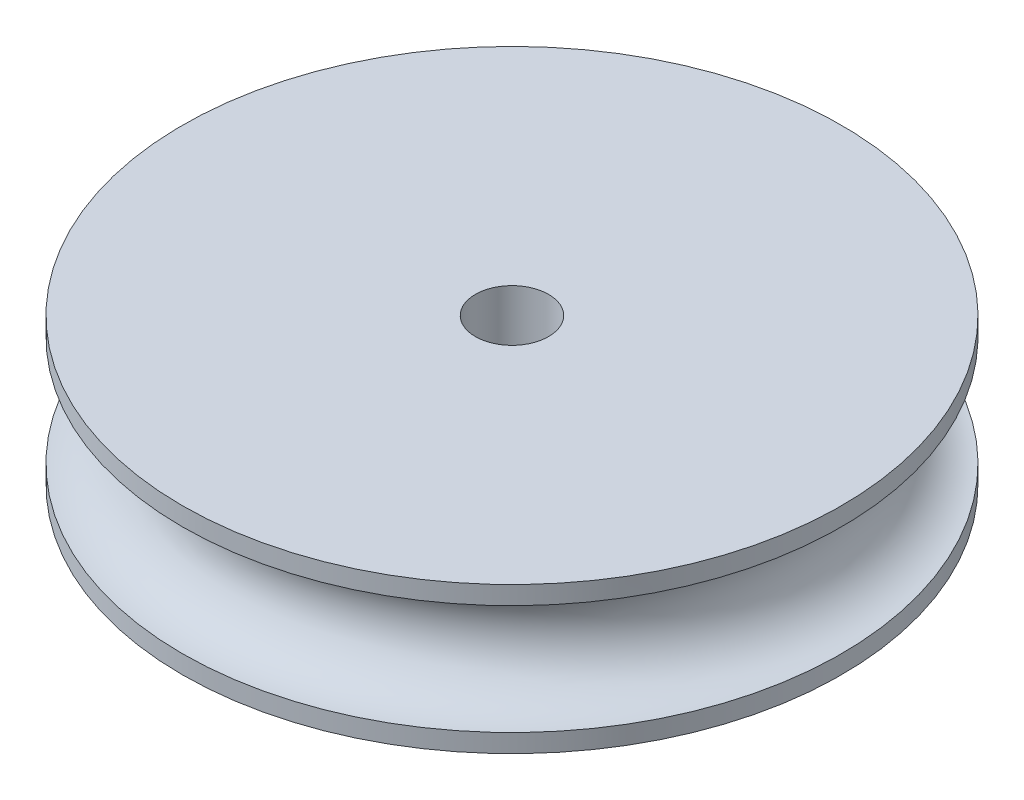
SolidWorks part; units mm, degrees
material "PET"
ref_plane "Front Plane" through (0, 0, 0) normal (0, 0, 1) x (1, 0, 0)
ref_plane "Top Plane" through (0, 0, 0) normal (0, 1, 0) x (1, 0, 0)
ref_plane "Right Plane" through (0, 0, 0) normal (1, 0, 0) x (0, 0, -1)
sketch "Sketch1" plane through (0, 50.573, 0) normal (0, 1, 0) x (1, 0, 0)
  circle A0 centre (0, -53) radius 9
  circle A1 centre (0, -53) radius 1
  dimension "D1" = 18
extrude "Boss-Extrude1" add sketch "Sketch1" against normal blind 4
sketch "Sketch2" plane through (0, 0, 0) normal (1, 0, 0) x (0, 0, -1)
  line L0 (-44, 46.573) -> (-44, 50.573) construction
  line L1 (-53, 46.573) -> (-53, 55.6007) construction
  line L2 (-62, 46.573) -> (-44, 46.573) construction
  circle A0 centre (-44, 48.573) radius 1.5
  dimension "D1" = 3
revolve "Cut-Revolve1" cut sketch "Sketch2" angle 360 about L1
